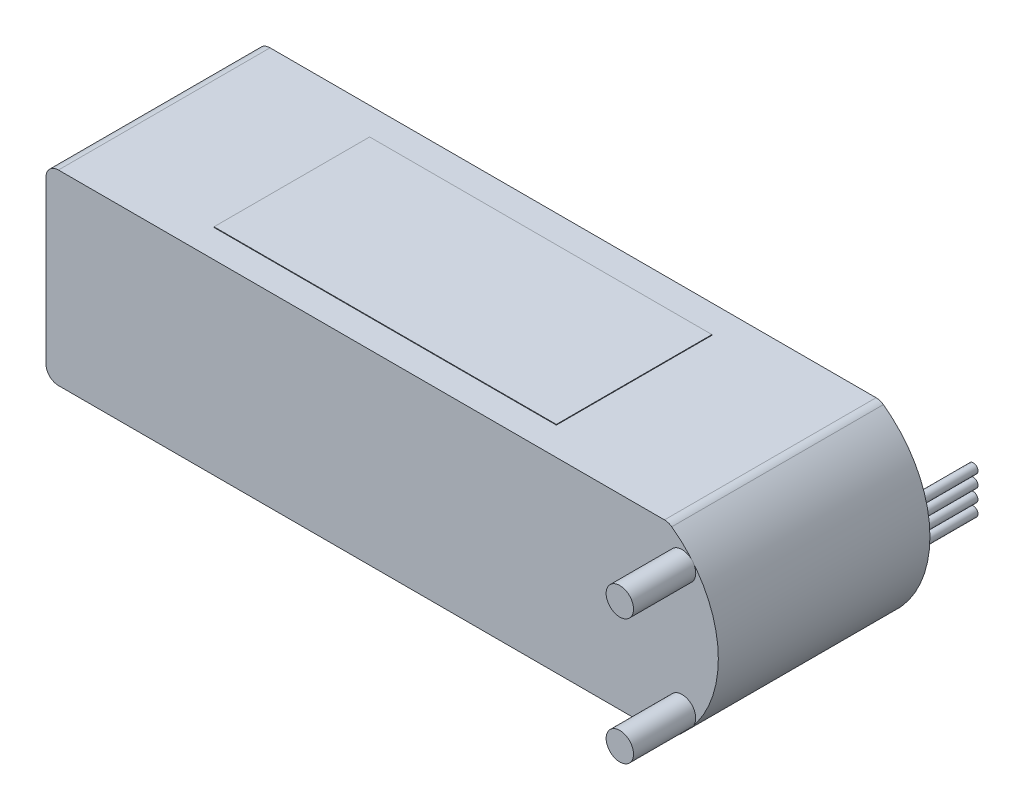
SolidWorks part; units mm, degrees
ref_plane "前视基准面" through (0, 0, 0) normal (0, 0, 1) x (1, 0, 0)
ref_plane "上视基准面" through (0, 0, 0) normal (0, 1, 0) x (1, 0, 0)
ref_plane "右视基准面" through (0, 0, 0) normal (1, 0, 0) x (0, 0, -1)
sketch "草图1" plane through (0, 0, 0) normal (0, 0, 1) x (1, 0, 0)
  line L1 (-50, 15) -> (50, 15)
  line L2 (-50, 15) -> (-50, -15)
  line L3 (-50, -15) -> (50, -15)
  line L4 (50, 15) -> (50, -15) construction
  line L5 (-50, 15) -> (50, -15) construction
  line L6 (-50, -15) -> (50, 15) construction
  arc A0 (50, -15) -> (50, 15) centre (40, 0) ccw
  point P0 (0, 0)
  dimension "D3" = 40
  dimension "D4" = 18.0278
  dimension "D1" = 100
  dimension "D2" = 30
extrude "凸台-拉伸1" add sketch "草图1" along normal mid plane 34
sketch "草图2" plane through (0, 0, 17) normal (0, 0, 1) x (1, 0, 0)
  line L0 (-5.271, 0) -> (17.0038, 0) construction
  line L1 (50, 21.8546) -> (50, -18.0902) construction
  circle A0 centre (52.2, 10.0835) radius 2.2
  circle A1 centre (52.2, -10.0835) radius 2.2
  arc A2 (50, -15) -> (50, 15) centre (40, 0) ccw construction
  dimension "D1" = 4.4
extrude "凸台-拉伸2" add sketch "草图2" along normal blind 10 separate body
sketch "草图3" plane through (0, 0, -17) normal (0, 0, -1) x (-1, 0, 0)
  line L0 (8.5368, 0) -> (-11.3095, 0) construction
  line L1 (-55, 10.0253) -> (-55, -12.4155) construction
  circle A0 centre (-55, 3) radius 0.75
  circle A1 centre (-55, 1) radius 0.75
  circle A2 centre (-55, -1) radius 0.75
  circle A3 centre (-55, -3) radius 0.75
  dimension "D1" = 1.5
  dimension "D2" = 2
  dimension "D3" = 6
  dimension "D4" = 5
extrude "凸台-拉伸3" add sketch "草图3" along normal blind 10 separate body
sketch "草图5" plane through (0, 15, 0) normal (0, 1, 0) x (1, 0, 0)
  line L1 (-27.5, 12.5) -> (27.5, 12.5)
  line L2 (-27.5, 12.5) -> (-27.5, -12.5)
  line L3 (-27.5, -12.5) -> (27.5, -12.5)
  line L4 (27.5, 12.5) -> (27.5, -12.5)
  line L5 (-27.5, 12.5) -> (27.5, -12.5) construction
  line L6 (-27.5, -12.5) -> (27.5, 12.5) construction
  point P0 (0, 0)
  dimension "D1" = 55
  dimension "D2" = 25
extrude "凸台-拉伸4" add sketch "草图5" along normal blind 0.1
fillet "圆角1" radius 2 4 edges at (50, -15, 0) (50, 15, 0) (-50, -15, 0) (-50, 15, 0)
